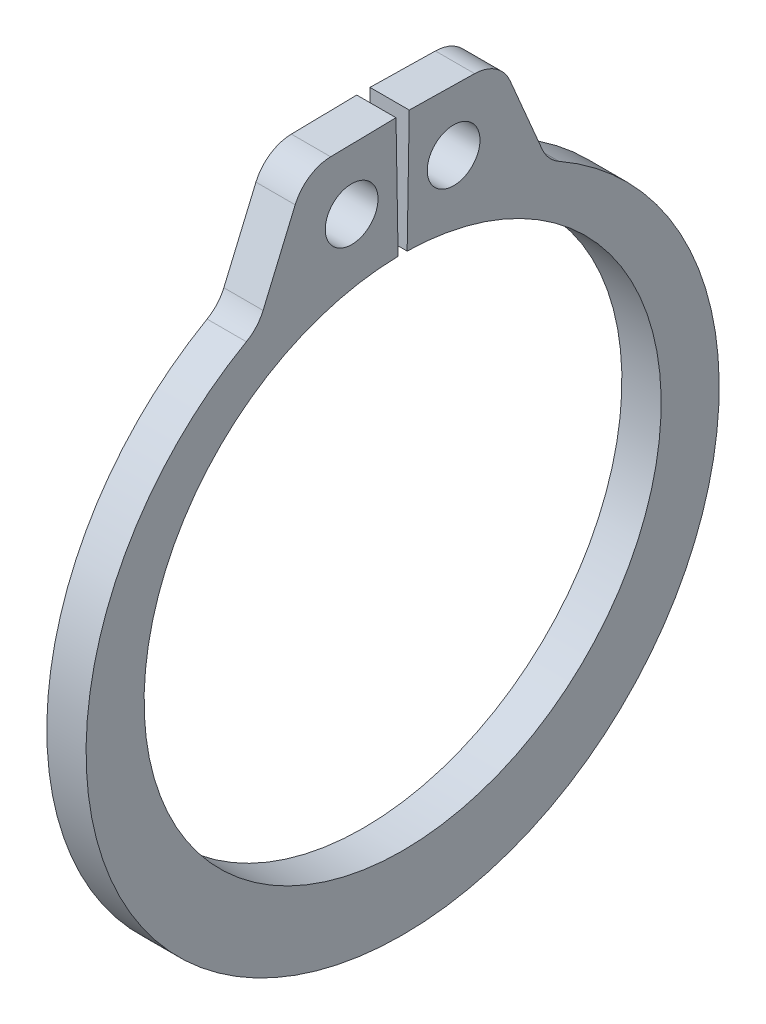
SolidWorks part; units mm, degrees
material "Cast Carbon Steel"
ref_plane "Front" through (0, 0, 0) normal (0, 0, 1) x (1, 0, 0)
ref_plane "Top" through (0, 0, 0) normal (0, 1, 0) x (1, 0, 0)
ref_plane "Right" through (0, 0, 0) normal (1, 0, 0) x (0, 0, -1)
sketch "Sketch1" plane through (0, 0, 0) normal (1, 0, 0) x (0, 0, -1)
  line L0 (0, 0) -> (0, 5.8547) construction
  line L1 (-0.1022, 5.8538) -> (-0.1501, 8.5966)
  line L2 (0.1501, 8.5966) -> (2.2071, 8.5607)
  line L3 (2.2071, 8.5607) -> (3.2813, 6.0365)
  line L4 (0.1022, 5.8538) -> (0.1501, 8.5966)
  line L5 (-0.1501, 8.5966) -> (-2.2071, 8.5607)
  line L6 (-2.2071, 8.5607) -> (-3.2813, 6.0365)
  line L7 (-3.2813, 6.0365) -> (-2.7961, 5.1439) construction
  line L8 (3.2813, 6.0365) -> (2.7961, 5.1439) construction
  line L9 (0, -5.8547) -> (0, -7.5057) construction
  line L10 (-2.2071, 8.5607) -> (-0.1022, 5.8538) construction
  line L11 (0, 5.8547) -> (0, 8.5979) construction
  line L12 (-5.8547, 0) -> (5.8547, 0) construction
  circle A0 centre (0, 0) radius 5.8547 construction
  arc A1 (-0.1022, 5.8538) -> (0.1022, 5.8538) centre (0, 0) ccw
  circle A3 centre (0, 0) radius 9.779 construction
  circle A4 centre (-1.1547, 7.2072) radius 0.5969
  circle A5 centre (1.1547, 7.2072) radius 0.5969
  arc A6 (-3.2813, 6.0365) -> (3.2813, 6.0365) centre (0, -0.3371) ccw
  point P0 (0, -7.5057)
  dimension "A" = 11.7094
  dimension "Hole" = 1.1938
  dimension "Smin" = 1.016
  dimension "H" = 2.7432
  dimension "D2" = 2.0574
  dimension "Angle" = 1
extrude "Extrude1" add sketch "Sketch1" along normal mid plane 0.889
fillet "Fillet1" radius 0.889 4 edges at (0, 6.0365, 3.2813) (0, 6.0365, -3.2813) (0, 8.5607, 2.2071) (0, 8.5607, -2.2071)
sketch "Sketch2" plane through (0, 0, 0) normal (0, 0, 1) x (1, 0, 0)
  line L0 (-4.9403, 0) -> (12.8397, 0)
  line L1 (12.8397, 0) -> (12.8397, -6.35)
  line L2 (-4.9403, 0) -> (-4.9403, -5.9436)
  line L3 (12.8397, -6.35) -> (0.4953, -6.35)
  line L4 (0.4953, -6.35) -> (0.4953, -5.9436)
  line L5 (0.4953, -5.9436) -> (-0.4953, -5.9436)
  line L6 (-0.4953, -5.9436) -> (-0.4953, -6.35)
  line L7 (-0.4953, -6.35) -> (-4.9403, -6.35) construction
  line L8 (-4.9403, -6.35) -> (-4.9403, 0) construction
  line L9 (12.8397, 0) -> (76.391, 0) construction
  line L10 (0, -5.9436) -> (0, 0) construction
  line L11 (-4.9403, -5.9436) -> (-4.5339, -6.35)
  line L12 (-4.5339, -6.35) -> (-0.4953, -6.35)
  dimension "D2" = 17.78
  dimension "D3" = 4.445
  dimension "D1" = 45
revolve "Revolve1" [suppressed] add sketch "Sketch2" angle 360 about L9
delete or keep bodies "Body-Delete1" [suppressed] type delete bodies bodies 122
equation "\"D2@Sketch2\" = \"D1@Extrude1\"*20"
equation "\"D3@Sketch2\" = \"D2@Sketch2\"/4"
equation "\"D2@Sketch1\" = \"H@Sketch1\"*.75"
equation "\"D1@Fillet1\" = \"D1@Extrude1\""
